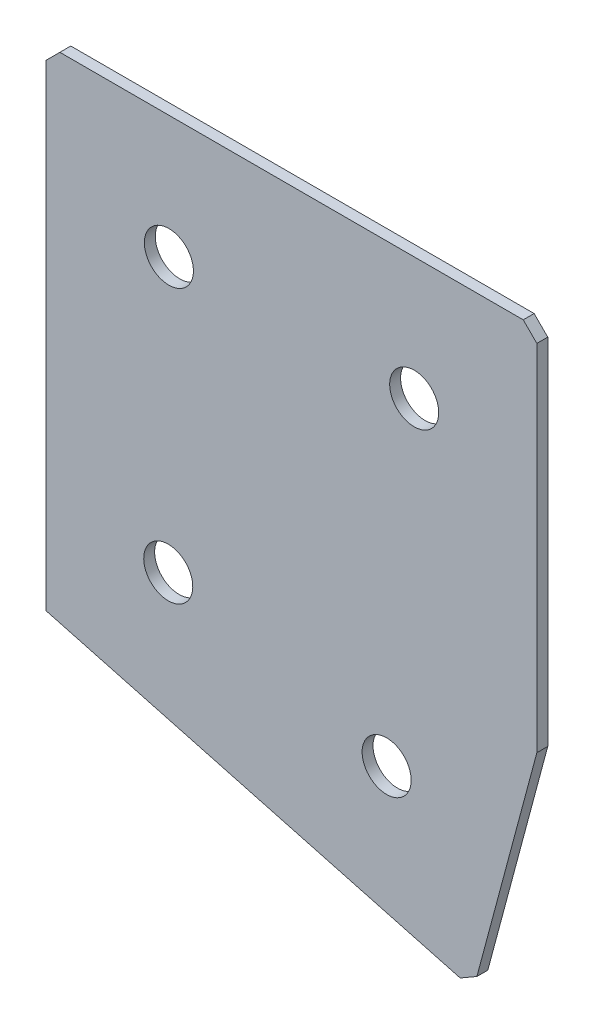
SolidWorks part; units mm, degrees
material "Простая углеродистая сталь"
ref_plane "Спереди" through (0, 0, 0) normal (0, 0, 1) x (1, 0, 0)
ref_plane "Сверху" through (0, 0, 0) normal (0, 1, 0) x (1, 0, 0)
ref_plane "Справа" through (0, 0, 0) normal (1, 0, 0) x (0, 0, -1)
sketch "Эскиз3" plane through (0, 0, 0) normal (0, 0, -1) x (1, 0, 0)
  line L0 (0, 0) -> (90, 0)
  line L1 (90, 0) -> (90, 67.528)
  line L2 (0, 0) -> (0, 90)
  line L3 (0, 90) -> (78.3531, 110.9947)
  line L4 (78.3531, 110.9947) -> (90, 67.528)
  dimension "D1" = 90
  dimension "D2" = 90
  dimension "D3" = 45
  dimension "D4" = 15
  dimension "D5" = 67.528
extrude "Бобышка-Вытянуть1" add sketch "Эскиз3" along normal blind 2
hole_wizard "Отверстие с зазором M81" positions "Эскиз4" profile "Эскиз5" hole size "M8" standard "DIN" end condition through all
sketch "Эскиз4" plane through (0, 0, -2) normal (0, 0, -1) x (1, 0, 0)
  line L0 (19.3185, 74.4709) -> (64.211, 86.4998) construction
  line L2 (78.3531, 110.9947) -> (0, 90) construction
  line L5 (0, 0) -> (90, 0) construction
  line L6 (0, 90) -> (0, 0) construction
  line L7 (90, 0) -> (90, 67.528) construction
  line L8 (90, 67.528) -> (78.3531, 110.9947) construction
  line L9 (19.3185, 74.4709) -> (0, 69.2945) construction
  line L10 (22.5, 22.5) -> (67.5, 22.5) construction
  line L12 (22.3804, 72.7031) -> (62.4432, 83.4379) construction
  line L13 (19.3185, 74.4709) -> (19.9656, 72.056) construction
  line L14 (19.9656, 72.056) -> (22.3804, 72.7031) construction
  point P31 (22.3804, 72.7031)
  point P33 (62.4432, 83.4379)
  point P35 (22.5, 22.5)
  point P37 (67.5, 22.5)
  point P55 (0, 0)
  point P56 (0, 0)
  point P57 (0, 0)
  point P58 (0, 0)
  point P59 (0, 0)
  dimension "D2" = 20
  dimension "D6" = 20
  dimension "D9" = 22.5
  dimension "D10" = 22.5
  dimension "D11" = 22.5
  dimension "D12" = 22.5
  dimension "D13" = 22.5
  dimension "D14" = 2.5
sketch "Эскиз5" plane through (67.5, -22.5, -2) normal (1, 0, 0) x (0, 1, 0)
  line L0 (0, 0) -> (0, 2)
  line L1 (0, 2) -> (4.5, 2)
  line L2 (4.5, 2) -> (4.5, 0)
  line L5 (4.5, 0) -> (0, 0)
  line L11 (0, -6.35) -> (0, 107.95) construction
  dimension "Диаметр сквозного отверстия" = 9
  dimension "Глубина сквозного отверстия" = 2
chamfer "Фаска1" distance 2.5 distance2 2.5 3 edges at (78.3531, -110.9947, -1) (90, 0, -1) (0, 0, -1)
